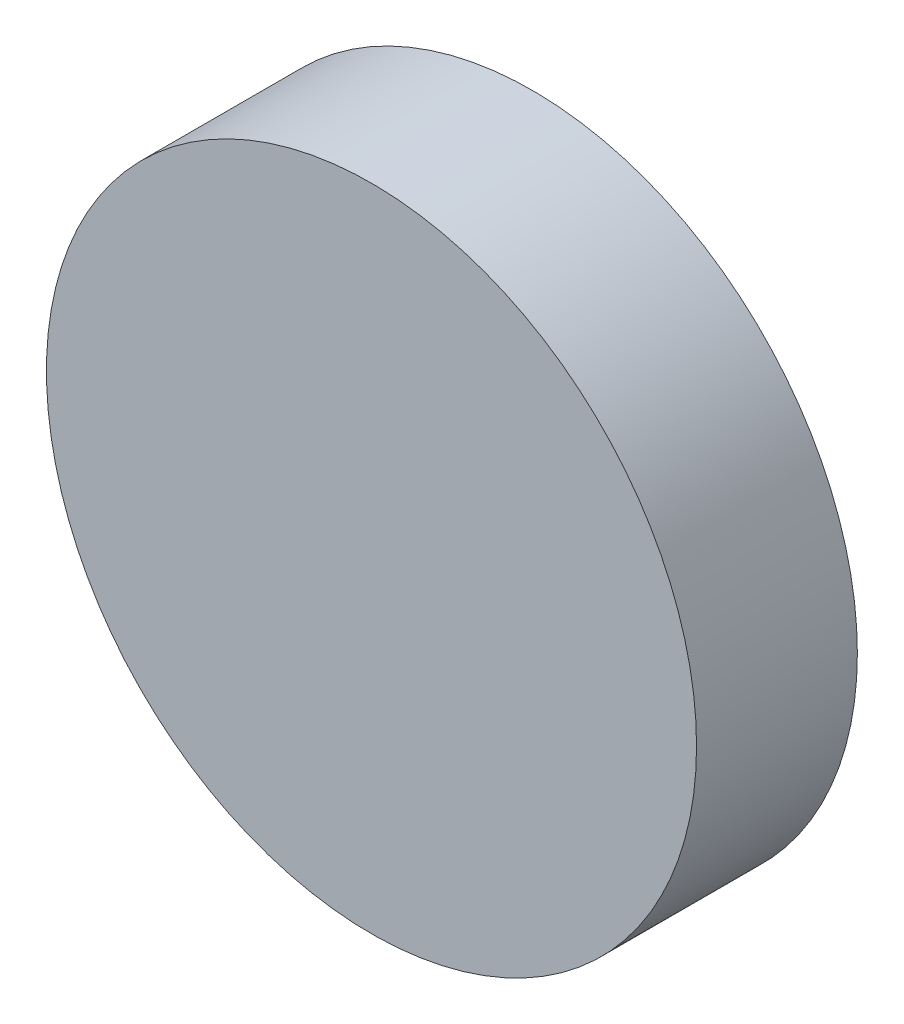
SolidWorks part; units mm, degrees
ref_plane "Front Plane" through (0, 0, 0) normal (0, 0, 1) x (1, 0, 0)
ref_plane "Top Plane" through (0, 0, 0) normal (0, 1, 0) x (1, 0, 0)
ref_plane "Right Plane" through (0, 0, 0) normal (1, 0, 0) x (0, 0, -1)
sketch "Sketch1" plane through (0, 0, 0) normal (0, 0, 1) x (1, 0, 0)
  circle A0 centre (0, 0) radius 6.0071
  dimension "D1" = 12.0142
extrude "Boss-Extrude1" add sketch "Sketch1" along normal blind 2.9718
sketch "Sketch3" plane through (0, 0, 2.9718) normal (0, 0, 1) x (1, 0, 0)
  line L0 (0, 0) -> (0, -6.0071) construction
  circle A0 centre (0, 0) radius 6.0071 construction
  point P0 (0, 0)
sketch "Sketch4" plane through (0, 0, 0) normal (0, 0, -1) x (-1, 0, 0)
  circle A0 centre (0, 0) radius 6.0071 construction
  point P0 (0, 0)
  point P1 (0, 0)
ref_plane "Plane1" through (0, 0, 0) normal (1, 0, 0) x (0, 0, -1)
sketch "Sketch8" plane through (0, 0, 0) normal (1, 0, 0) x (0, 0, -1)
  line L0 (0, 0) -> (-10.6549, 0)
